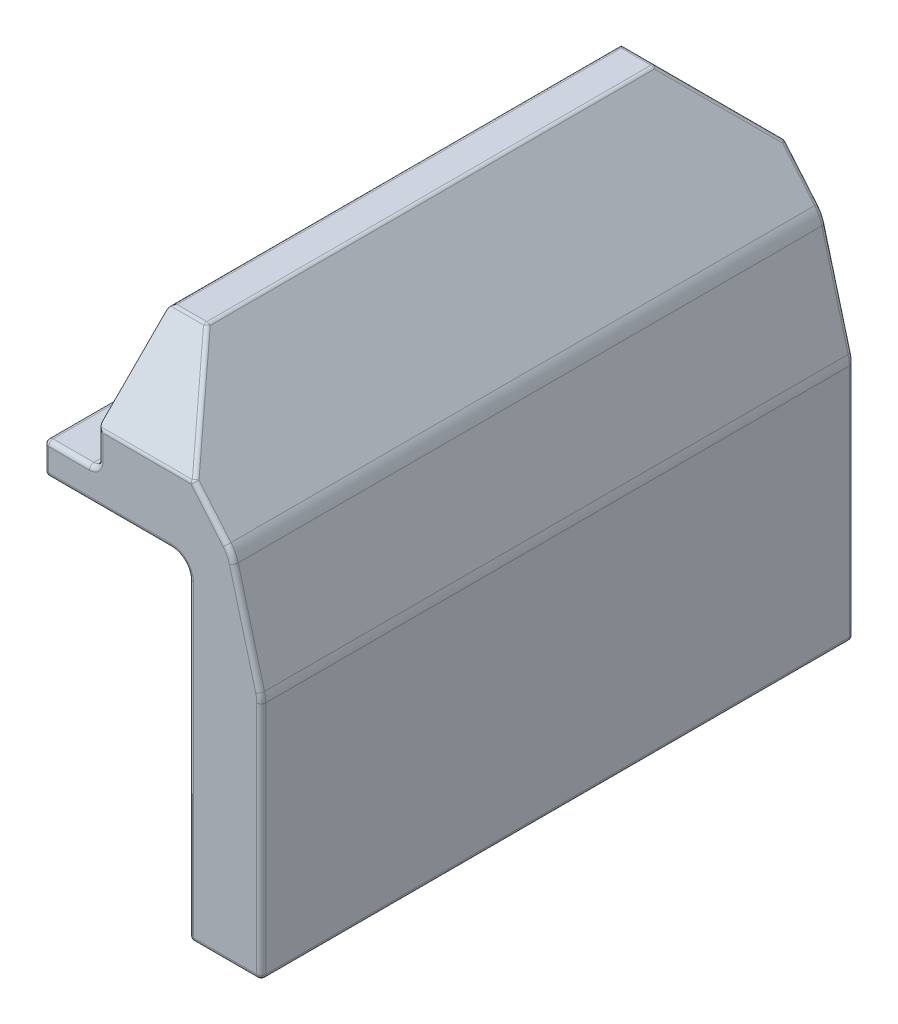
SolidWorks part; units mm, degrees
material "Delrin (Acetal)"
ref_plane "Front Plane" through (0, 0, 0) normal (0, 0, 1) x (1, 0, 0)
ref_plane "Top Plane" through (0, 0, 0) normal (0, 1, 0) x (1, 0, 0)
ref_plane "Right Plane" through (0, 0, 0) normal (1, 0, 0) x (0, 0, -1)
sketch "Sketch1" plane through (0, 0, 0) normal (0, 0, 1) x (1, 0, 0)
  line L1 (-38.1, 82.55) -> (38.1, 82.55)
  line L2 (-38.1, 82.55) -> (-38.1, -82.55)
  line L3 (-38.1, -82.55) -> (38.1, -82.55)
  line L4 (38.1, 82.55) -> (38.1, -82.55)
  line L5 (-38.1, 82.55) -> (38.1, -82.55) construction
  line L6 (-38.1, -82.55) -> (38.1, 82.55) construction
  point P0 (0, 0)
  dimension "Width" = 76.2
  dimension "Height" = 165.1
extrude "Extrude1" add sketch "Sketch1" along normal mid plane 207.9625
sketch "Sketch3" plane through (0, 0, 103.9813) normal (0, 0, 1) x (1, 0, 0)
  line L0 (-38.1, 82.55) -> (-38.1, -82.55) construction
  line L1 (-38.1, 33.3375) -> (12.7, 33.3375)
  line L2 (-38.1, 33.3375) -> (-38.1, -82.55)
  line L3 (-38.1, -82.55) -> (12.7, -82.55)
  line L4 (12.7, 33.3375) -> (12.7, -82.55)
  line L5 (-38.1, -82.55) -> (38.1, -82.55) construction
  line L6 (38.1, 82.55) -> (-38.1, 82.55) construction
  line L7 (38.1, -82.55) -> (38.1, 82.55) construction
  dimension "D1" = 49.2125
  dimension "D2" = 25.4
extrude "Cut-Extrude2" cut sketch "Sketch3" against normal up to next
sketch "Sketch10" plane through (0, 0, 103.9813) normal (0, 0, 1) x (1, 0, 0)
  line L0 (-6.35, 82.55) -> (27.7069, 41.9626)
  line L1 (-38.1, 44.45) -> (-22.225, 44.45)
  line L2 (-38.1, 44.45) -> (-38.1, 82.55)
  line L3 (-38.1, 82.55) -> (-19.05, 82.55)
  line L4 (-19.05, 47.625) -> (-19.05, 82.55)
  line L5 (38.1, 82.55) -> (-38.1, 82.55) construction
  line L6 (27.7069, 41.9626) -> (38.1, 3.175)
  line L7 (38.1, -82.55) -> (38.1, 82.55) construction
  line L8 (38.1, 3.175) -> (38.1, 82.55)
  line L9 (38.1, 82.55) -> (-6.35, 82.55)
  line L10 (12.7, -82.55) -> (38.1, -82.55) construction
  arc A0 (-19.05, 47.625) -> (-22.225, 44.45) centre (-22.225, 47.625) cw
  dimension "D7" = 3.175
  dimension "D1" = 38.1
  dimension "D2" = 130
  dimension "D3" = 155
  dimension "D4" = 85.725
  dimension "D5" = 12.7
  dimension "D6" = 31.75
extrude "Cut-Extrude6" cut sketch "Sketch10" against normal up to next
sketch "Sketch11" plane through (0, 0, 103.9813) normal (0, 0, 1) x (1, 0, 0)
  line L0 (15.875, 82.55) -> (38.1, 82.55)
  line L1 (-38.1, 82.55) -> (3.175, 82.55)
  line L2 (-38.1, 82.55) -> (-38.1, 44.45)
  line L3 (-38.1, 44.45) -> (0, 44.45)
  line L4 (3.175, 82.55) -> (3.175, 47.625)
  line L5 (-6.35, 82.55) -> (-19.05, 82.55) construction
  line L6 (38.1, 82.55) -> (38.1, 22.225)
  line L7 (38.1, -82.55) -> (38.1, 3.175) construction
  line L8 (38.1, 22.225) -> (24.7794, 71.9381)
  line L9 (24.7794, 71.9381) -> (15.875, 82.55)
  line L10 (12.7, -82.55) -> (38.1, -82.55) construction
  line L12 (-38.1, 44.45) -> (-38.1, 33.3375) construction
  line L13 (-38.1, 44.45) -> (-38.1, 33.3375) construction
  arc A0 (3.175, 47.625) -> (0, 44.45) centre (0, 47.625) cw
  dimension "D7" = 3.175
  dimension "D1" = 22.225
  dimension "D2" = 130
  dimension "D3" = 155
  dimension "D4" = 38.1
  dimension "D5" = 104.775
  dimension "D6" = 12.7
extrude "Cut-Extrude7" [suppressed] cut sketch "Sketch11" against normal up to next
hole_wizard "17/64 (0.26563) Diameter Hole2" [suppressed] positions "Sketch12" profile "Sketch13" hole size "17/64" standard "ANSI Inch"
sketch "Sketch12" [suppressed] plane through (0, 44.45, 0) normal (0, 1, 0) x (1, 0, 0)
  line L0 (-26.9875, 19.05) -> (-26.9875, -19.05) construction
  line L2 (-38.1, 103.9813) -> (-38.1, -103.9813) construction
  point P0 (-26.9875, 19.05)
  point P2 (-26.9875, -19.05)
  point P9 (-26.9875, 0)
  dimension "D1" = 11.1125
  dimension "D2" = 38.1
sketch "Sketch13" plane through (-26.9875, 44.45, -19.05) normal (1, 0, 0) x (0, 0, 1)
  line L0 (0, 0) -> (0, 11.1125)
  line L1 (0, 11.1125) -> (3.3735, 11.1125)
  line L2 (3.3735, 11.1125) -> (3.3735, 0)
  line L5 (3.3735, 0) -> (0, 0)
  line L11 (0, -6.35) -> (0, 107.95) construction
  dimension "Thru Hole Dia." = 6.747
  dimension "Thru Hole Depth" = 11.1125
chamfer "Chamfer1" distance 25.4 angle 45 2 edges at (-12.7, 82.55, 103.9813) (-12.7, 82.55, -103.9813)
chamfer "Chamfer2" [suppressed] distance 25.4 angle 45
fillet "Fillet5" radius 6.35 1 edges at (12.7, 33.3375, 0)
shell "Shell2" thickness 6.35
sketch "Sketch16" plane through (0, -82.55, 0) normal (0, -1, 0) x (1, 0, 0)
  line L0 (19.05, -97.6313) -> (19.05, 97.6313) construction
  line L1 (19.05, 3.175) -> (31.75, 3.175)
  line L2 (19.05, 3.175) -> (19.05, -3.175)
  line L3 (19.05, -3.175) -> (31.75, -3.175)
  line L4 (31.75, 3.175) -> (31.75, -3.175)
  line L7 (31.75, 97.6313) -> (31.75, -97.6313) construction
  point P11 (19.05, 0)
  dimension "D1" = 6.35
extrude "Boss-Extrude1" add sketch "Sketch16" against normal up to body separate body
hole_wizard "17/64 (0.26563) Diameter Hole3" positions "Sketch14" profile "Sketch15" hole size "17/64" standard "ANSI Inch" end condition up to next
sketch "Sketch14" plane through (0, 44.45, 0) normal (0, 1, 0) x (1, 0, 0)
  line L0 (-26.9875, 19.05) -> (-26.9875, -19.05) construction
  line L2 (-38.1, 103.9813) -> (-38.1, -103.9813) construction
  point P0 (-26.9875, 19.05)
  point P2 (-26.9875, -19.05)
  point P8 (-26.9875, 0)
  dimension "D1" = 11.1125
  dimension "D2" = 38.1
sketch "Sketch15" plane through (-26.9875, 44.45, -19.05) normal (1, 0, 0) x (0, 0, 1)
  line L0 (0, 0) -> (0, 11.1125)
  line L1 (0, 11.1125) -> (3.3735, 11.1125)
  line L2 (3.3735, 11.1125) -> (3.3735, 0)
  line L5 (3.3735, 0) -> (0, 0)
  line L11 (0, -6.35) -> (0, 107.95) construction
  dimension "Thru Hole Dia." = 6.747
  dimension "Thru Hole Depth" = 11.1125
fillet "Fillet1" radius 12.7 2 edges at (38.1, 3.175, 0) (27.7069, 41.9626, 0)
fillet "Fillet2" [suppressed] radius 12.7
fillet "Fillet3" [suppressed] radius 1.5875
fillet "Fillet4" radius 1.5875 58 edges at (12.7, -27.7812, 103.9813) (12.7, -27.7812, -103.9813) (-19.05, 52.3875, 103.9813) (-19.9799, 45.3799, 103.9813) (-19.05, 52.3875, -103.9813) (-19.9799, 45.3799, -103.9813) (38.1, -40.5235, -103.9813) (37.9913, 3.1607, -103.9813) (33.0514, 22.0165, -103.9813) (27.4334, 41.8202, -103.9813) (38.1, -40.5235, 103.9813) (37.9913, 3.1607, 103.9813) (33.0514, 22.0165, 103.9813) (27.4334, 41.8202, 103.9813) (-30.1625, 44.45, 103.9813) (-30.1625, 44.45, -103.9813) (-26.9875, 44.45, 22.4235) (-26.9875, 44.45, -15.6765) (-38.1, 38.8938, -103.9813) (-38.1, 44.45, 0) (-38.1, 38.8937, 103.9813) (-38.1, 33.3375, 0) (-15.875, 33.3375, 103.9813) (-15.875, 33.3375, -103.9813) (-26.9875, 33.3375, 22.4235) (-26.9875, 33.3375, -15.6765) (38.1, -82.55, 0) (25.4, -82.55, -103.9813) (12.7, -82.55, 0) (25.4, -82.55, 103.9813) (25.4, -82.55, -97.6313) (31.75, -82.55, 50.4031) (31.75, -82.55, -50.4031) (25.4, -82.55, 97.6313) (19.05, -82.55, 50.4031) (19.05, -82.55, -50.4031) (20.4301, 50.6347, -103.9813) (20.4301, 50.6347, 103.9813) (-6.35, 82.55, 0) (-19.05, 82.55, 0) (-12.7, 76.2, 0) (19.05, -27.7812, -97.6313) (19.05, -27.7812, 97.6313) (-5.3049, 39.6875, -97.6313) (-5.3049, 39.6875, 97.6313) (-16.9599, 39.6875, 0) (4.3066, 69.85, 91.2812) (4.3066, 69.85, -91.2812) (-12.7, 82.55, -78.5812) (-12.7, 82.55, 78.5812) (-2.0434, 57.15, -103.9813) (-2.0434, 57.15, 103.9813) (15.3303, 35.9678, -97.6313) (15.3303, 35.9678, 97.6313) (10.8401, 31.4776, -103.9813) (10.8401, 31.4776, 103.9813) (25.4, -82.55, -3.175) (25.4, -82.55, 3.175)
